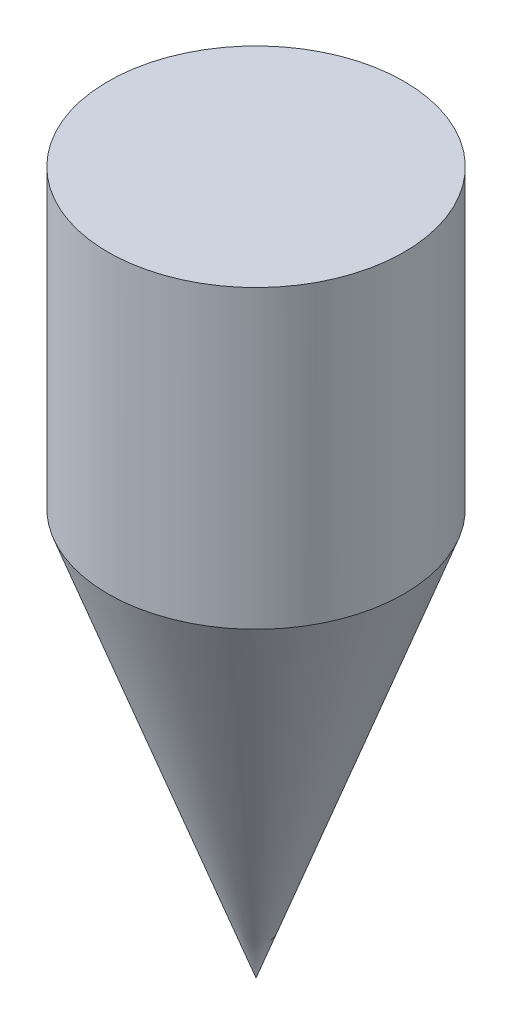
SolidWorks part; units mm, degrees
ref_plane "Front Plane" through (0, 0, 0) normal (0, 0, 1) x (1, 0, 0)
ref_plane "Top Plane" through (0, 0, 0) normal (0, 1, 0) x (1, 0, 0)
ref_plane "Right Plane" through (0, 0, 0) normal (1, 0, 0) x (0, 0, -1)
sketch "Sketch1" plane through (0, 0, 0) normal (0, 0, 1) x (1, 0, 0)
  line L0 (0, 0) -> (0, 86.3723) construction
  line L1 (-5, 37.1837) -> (-5, 27.1837)
  line L2 (-5, 37.1837) -> (0, 37.1837)
  line L3 (-5, 27.1837) -> (0, 13.4463)
  line L4 (0, 13.4463) -> (0, 37.1837)
  dimension "D1" = 160
  dimension "D2" = 10
  dimension "D3" = 5
revolve "Revolve1" add sketch "Sketch1" angle 360 about L0
